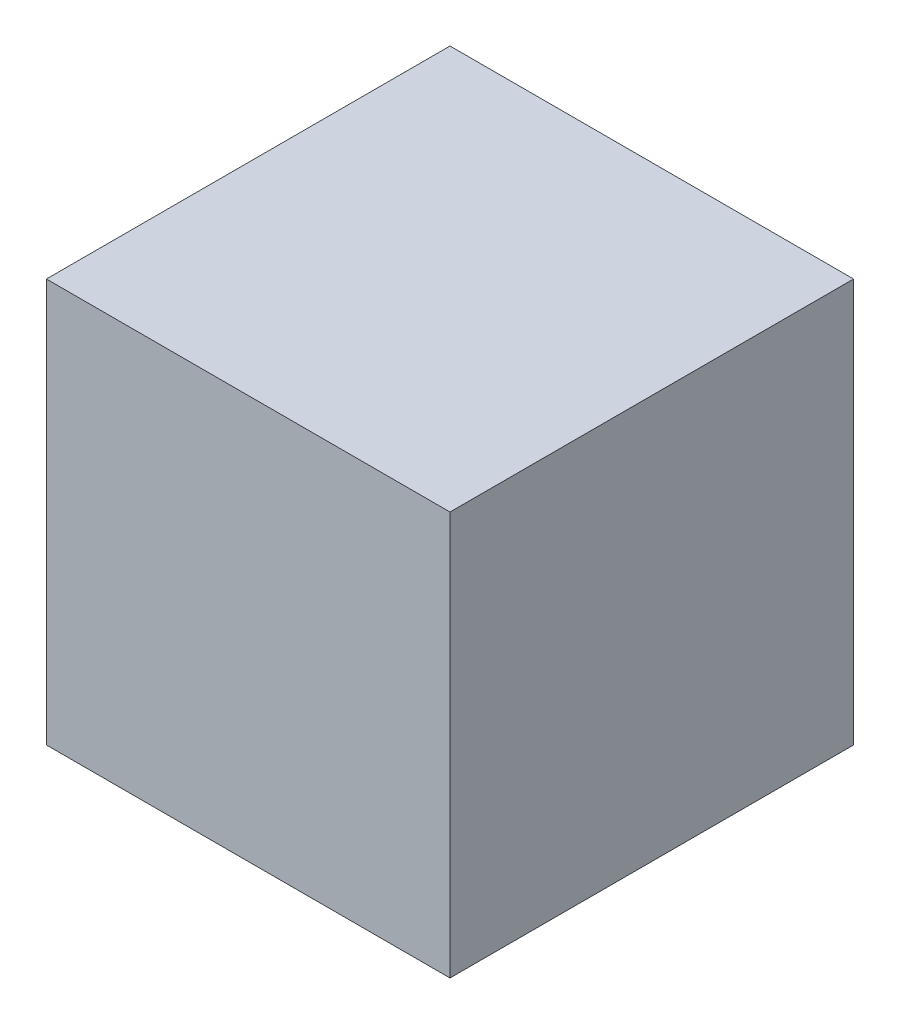
SolidWorks part; units mm, degrees
ref_plane "Front Plane" through (0, 0, 0) normal (0, 0, 1) x (1, 0, 0)
ref_plane "Top Plane" through (0, 0, 0) normal (0, 1, 0) x (1, 0, 0)
ref_plane "Right Plane" through (0, 0, 0) normal (1, 0, 0) x (0, 0, -1)
sketch "Sketch1" plane through (0, 0, 0) normal (0, 1, 0) x (1, 0, 0)
  line L1 (-25, 25) -> (25, 25)
  line L2 (-25, 25) -> (-25, -25)
  line L3 (-25, -25) -> (25, -25)
  line L4 (25, 25) -> (25, -25)
  line L5 (-25, 25) -> (25, -25) construction
  line L6 (-25, -25) -> (25, 25) construction
  point P0 (0, 0)
  dimension "D1" = 50
  dimension "D2" = 50
extrude "Boss-Extrude1" add sketch "Sketch1" along normal blind 50
